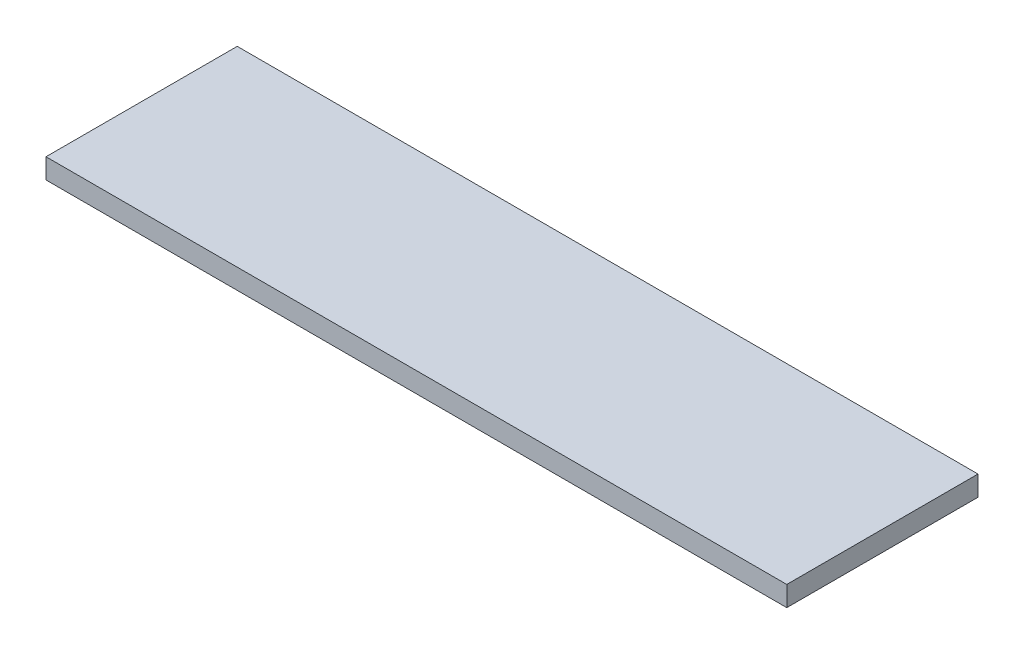
SolidWorks part; units mm, degrees
ref_plane "Front Plane" through (0, 0, 0) normal (0, 0, 1) x (1, 0, 0)
ref_plane "Top Plane" through (0, 0, 0) normal (0, 1, 0) x (1, 0, 0)
ref_plane "Right Plane" through (0, 0, 0) normal (1, 0, 0) x (0, 0, -1)
sketch "Sketch1" plane through (0, 0, 0) normal (0, 1, 0) x (1, 0, 0)
  line L1 (-184, -47.5) -> (184, -47.5)
  line L2 (-184, -47.5) -> (-184, 47.5)
  line L3 (-184, 47.5) -> (184, 47.5)
  line L4 (184, -47.5) -> (184, 47.5)
  line L5 (-184, -47.5) -> (184, 47.5) construction
  line L6 (-184, 47.5) -> (184, -47.5) construction
  point P0 (0, 0)
  dimension "D1" = 368
  dimension "D2" = 95
extrude "Boss-Extrude1" add sketch "Sketch1" along normal blind 10
sketch "Sketch2" plane through (0, 10, 0) normal (0, 1, 0) x (1, 0, 0)
  line L0 (-184, 0) -> (184, 0) construction
  line L1 (-184, 47.5) -> (-184, -47.5) construction
  line L2 (184, -47.5) -> (184, 47.5) construction
  line L3 (-184, -45) -> (125, -45) construction
  line L4 (-184, 45) -> (125, 45) construction
  dimension "D1" = 45
